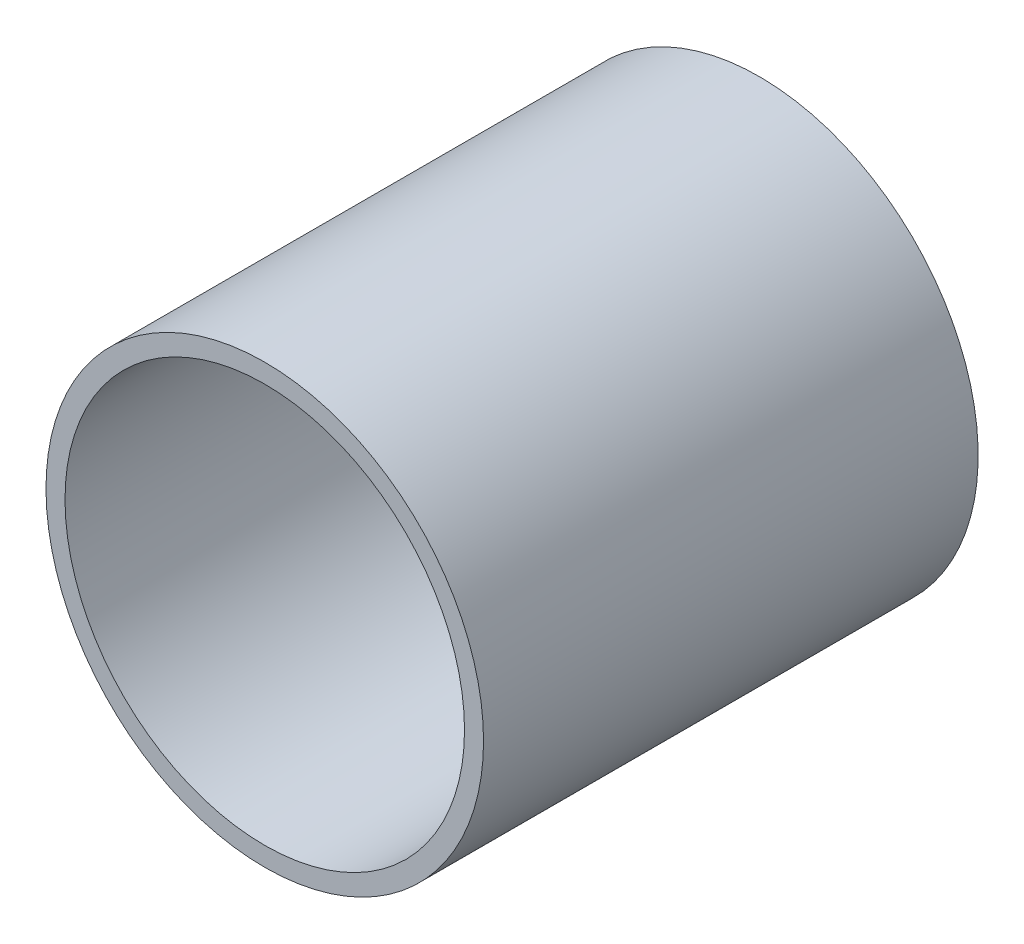
SolidWorks part; units mm, degrees
material "Glass"
ref_plane "Front Plane" through (0, 0, 0) normal (0, 0, 1) x (1, 0, 0)
ref_plane "Top Plane" through (0, 0, 0) normal (0, 1, 0) x (1, 0, 0)
ref_plane "Right Plane" through (0, 0, 0) normal (1, 0, 0) x (0, 0, -1)
sketch "Sketch2" plane through (0, 0, 0) normal (0, 0, 1) x (1, 0, 0)
  circle A0 centre (0, 0) radius 115
  circle A1 centre (0, 0) radius 105
  dimension "D1" = 10
  dimension "D2" = 230
extrude "Boss-Extrude1" add sketch "Sketch2" along normal blind 260
sketch "Sketch3" plane through (0, 0, 0) normal (1, 0, 0) x (0, 0, -1)
  line L0 (0, -115) -> (0, 115) construction
  line L1 (0, 7.5) -> (-2, 7.5)
  line L2 (0, 7.5) -> (0, -7.5)
  line L3 (0, -7.5) -> (-2, -7.5)
  line L4 (-2, 7.5) -> (-2, -7.5)
  line L5 (0, 115) -> (-260, 115) construction
  dimension "D1" = 107.5
  dimension "D2" = 15
  dimension "D3" = 2
extrude "Cut-Extrude1" cut sketch "Sketch3" against normal up to next
